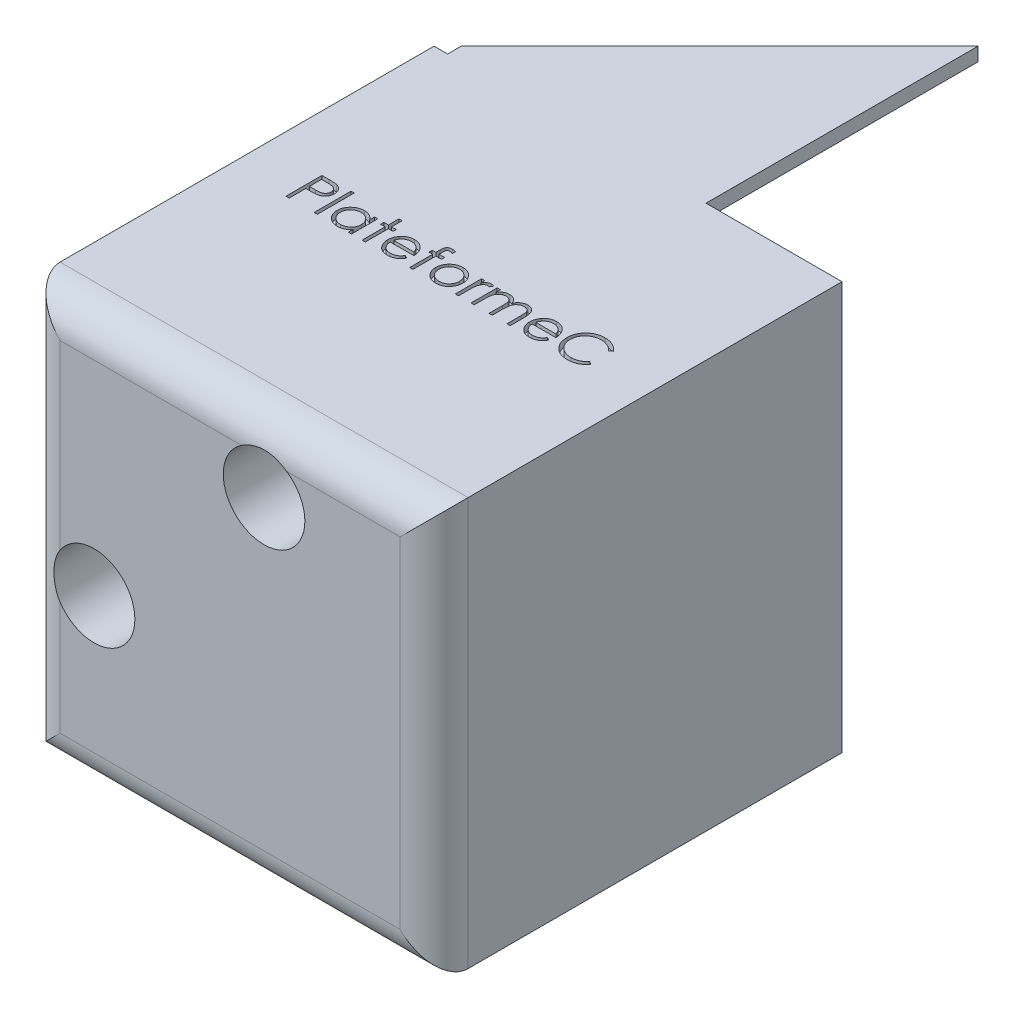
SolidWorks part; units mm, degrees
ref_plane "Plan de face" through (0, 0, 0) normal (0, 0, 1) x (1, 0, 0)
ref_plane "Plan de dessus" through (0, 0, 0) normal (0, 1, 0) x (1, 0, 0)
ref_plane "Plan de droite" through (0, 0, 0) normal (1, 0, 0) x (0, 0, -1)
sketch "Esquisse1" plane through (0, 0, 0) normal (0, 0, 1) x (1, 0, 0)
  line L1 (0, 0) -> (-60, 0)
  line L2 (0, 0) -> (0, 60)
  line L3 (0, 60) -> (-60, 60)
  line L4 (-60, 0) -> (-60, 60)
  dimension "D1" = 60
  dimension "D2" = 60
extrude "Boss.-Extru.1" add sketch "Esquisse1" along normal blind 60
sketch "Esquisse3" plane through (0, 0, 0) normal (0, 0, -1) x (-1, 0, 0)
  line L0 (60, 60) -> (60, 20)
  line L1 (60, 60) -> (60, 0) construction
  line L2 (60, 20) -> (58, 20)
  line L3 (58, 20) -> (58, 58)
  line L4 (58, 58) -> (20, 58)
  line L5 (20, 58) -> (20, 60)
  line L6 (0, 60) -> (60, 60) construction
  line L7 (20, 60) -> (60, 60)
  dimension "D1" = 40
  dimension "D2" = 40
  dimension "D3" = 2
  dimension "D4" = 2
extrude "Boss.-Extru.3" add sketch "Esquisse3" along normal blind 40
sketch "Esquisse6" plane through (-60, 0, 0) normal (-1, 0, 0) x (0, 0, 1)
  line L0 (30, 0) -> (30, 60) construction
  line L1 (60, 0) -> (0, 0) construction
  line L2 (60, 60) -> (-40, 60) construction
  text T0 "PING" font "Century Gothic" height in points 48
extrude "Enlèv. mat.-Extru.3" cut sketch "Esquisse6" against normal blind 1
sketch "Esquisse7" plane through (0, 60, 0) normal (0, 1, 0) x (1, 0, 0)
  line L0 (0, -30) -> (-60, -30) construction
  line L1 (0, -60) -> (0, 0) construction
  line L2 (-60, -60) -> (-60, 40) construction
  text T0 "PlateformeC" font "Century Gothic" height in points 20
extrude "Enlèv. mat.-Extru.4" cut sketch "Esquisse7" against normal blind 1
sketch "Esquisse8" plane through (-60, 0, 0) normal (-1, 0, 0) x (0, 0, 1)
  line L0 (-40, 20) -> (0, 60)
  line L1 (60, 60) -> (-40, 60) construction
  line L2 (0, 60) -> (-40, 60)
  line L3 (-40, 60) -> (-40, 20)
  dimension "D1" = 45
extrude "Enlèv. mat.-Extru.5" cut sketch "Esquisse8" against normal blind 2
sketch "Esquisse11" plane through (0, 60, 0) normal (0, 1, 0) x (1, 0, 0)
  line L0 (-20, 40) -> (-60, 0)
  line L1 (-60, 0) -> (-61.461, 41.461)
  line L2 (-61.461, 41.461) -> (-20, 40)
extrude "Enlèv. mat.-Extru.6" cut sketch "Esquisse11" against normal blind 2
fillet "Congé1" radius 5 4 edges at (-30, 0, 60) (0, 30, 60) (-60, 30, 60) (-30, 60, 60)
sketch "Esquisse13" plane through (0, 0, 60) normal (0, 0, 1) x (1, 0, 0)
  line L0 (-60, 60) -> (0, 60) construction
  line L1 (-60, 0) -> (-60, 60) construction
  circle A0 centre (-50, 25) radius 3
  circle A1 centre (-25, 50) radius 3
  dimension "D1" = 6
  dimension "D2" = 6
  dimension "D3" = 10
  dimension "D4" = 10
  dimension "D5" = 35
  dimension "D6" = 35
extrude "Enlèv. mat.-Extru.7" cut sketch "Esquisse13" against normal through all
sketch "Esquisse14" plane through (0, 0, 60) normal (0, 0, 1) x (1, 0, 0)
  circle A0 centre (-50, 25) radius 6
  circle A1 centre (-25, 50) radius 6
  dimension "D1" = 12
  dimension "D2" = 12
extrude "Enlèv. mat.-Extru.8" cut sketch "Esquisse14" against normal blind 54
